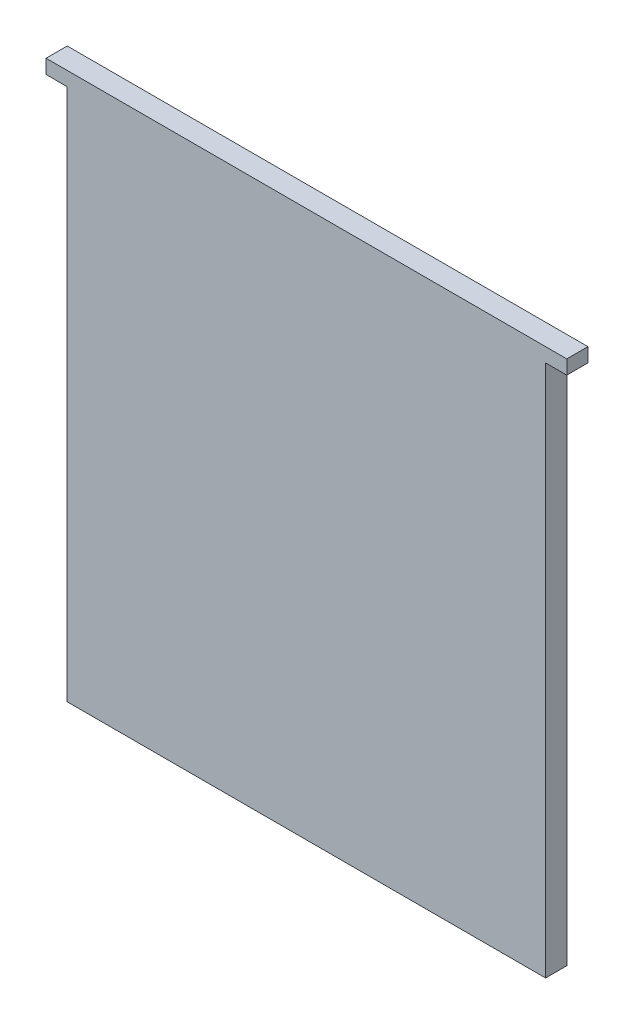
SolidWorks part; units mm, degrees
ref_plane "Plano frontal" through (0, 0, 0) normal (0, 0, 1) x (1, 0, 0)
ref_plane "Plano superior" through (0, 0, 0) normal (0, 1, 0) x (1, 0, 0)
ref_plane "Plano direito" through (0, 0, 0) normal (1, 0, 0) x (0, 0, -1)
sketch "Esboço1" plane through (0, 0, 0) normal (0, 0, 1) x (1, 0, 0)
  line L1 (-33.9, -38.75) -> (33.9, -38.75)
  line L2 (-33.9, -38.75) -> (-33.9, 38.75)
  line L3 (-33.9, 38.75) -> (33.9, 38.75)
  line L4 (33.9, -38.75) -> (33.9, 38.75)
  line L5 (-33.9, -38.75) -> (33.9, 38.75) construction
  line L6 (-33.9, 38.75) -> (33.9, -38.75) construction
  point P0 (0, 0)
  dimension "D1" = 77.5
  dimension "D2" = 67.8
extrude "Ressalto-extrusão1" add sketch "Esboço1" along normal blind 3
sketch "Esboço2" plane through (0, 0, 3) normal (0, 0, 1) x (1, 0, 0)
  line L0 (0, 53.9244) -> (0, -45.3623) construction
  line L1 (33.9, 38.75) -> (36.9, 38.75)
  line L2 (33.9, 38.75) -> (33.9, 36.75)
  line L3 (33.9, 36.75) -> (36.9, 36.75)
  line L4 (36.9, 38.75) -> (36.9, 36.75)
  line L5 (-36.9, 38.75) -> (-36.9, 36.75)
  line L6 (-33.9, 36.75) -> (-36.9, 36.75)
  line L7 (-33.9, 38.75) -> (-33.9, 36.75)
  line L8 (-33.9, 38.75) -> (-36.9, 38.75)
  dimension "D1" = 2
  dimension "D2" = 3
extrude "Ressalto-extrusão2" add sketch "Esboço2" against normal blind 3
ref_plane "Plano1" through (0, 0, 1.5) normal (0, 0, -1) x (-1, 0, 0)
sketch "Esboço3" plane through (0, 0, 1.5) normal (0, 0, -1) x (-1, 0, 0)
  line L0 (-36.9, 37.75) -> (36.9, 37.75)
  line L1 (-36.9, 36.75) -> (-36.9, 38.75) construction
  line L2 (36.9, 38.75) -> (36.9, 36.75) construction
